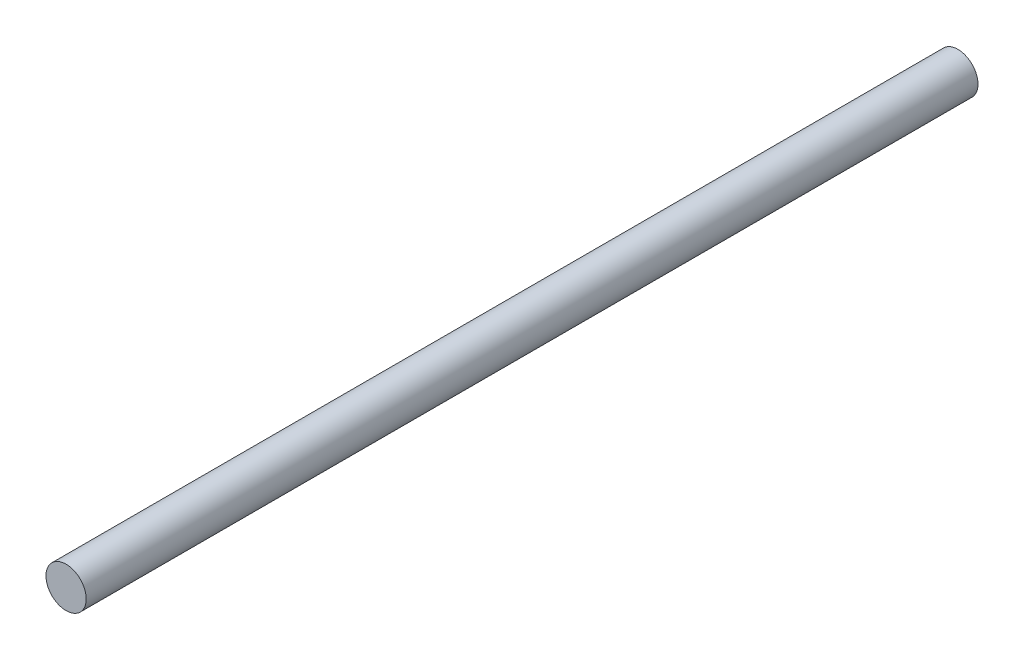
SolidWorks part; units mm, degrees
ref_plane "Front Plane" through (0, 0, 0) normal (0, 0, 1) x (1, 0, 0)
ref_plane "Top Plane" through (0, 0, 0) normal (0, 1, 0) x (1, 0, 0)
ref_plane "Right Plane" through (0, 0, 0) normal (1, 0, 0) x (0, 0, -1)
sketch "Sketch1" plane through (0, 0, 0) normal (0, 0, 1) x (1, 0, 0)
  circle A0 centre (0, 0) radius 7.9
  dimension "D1" = 15.8
extrude "Boss-Extrude1" add sketch "Sketch1" along normal blind 350
